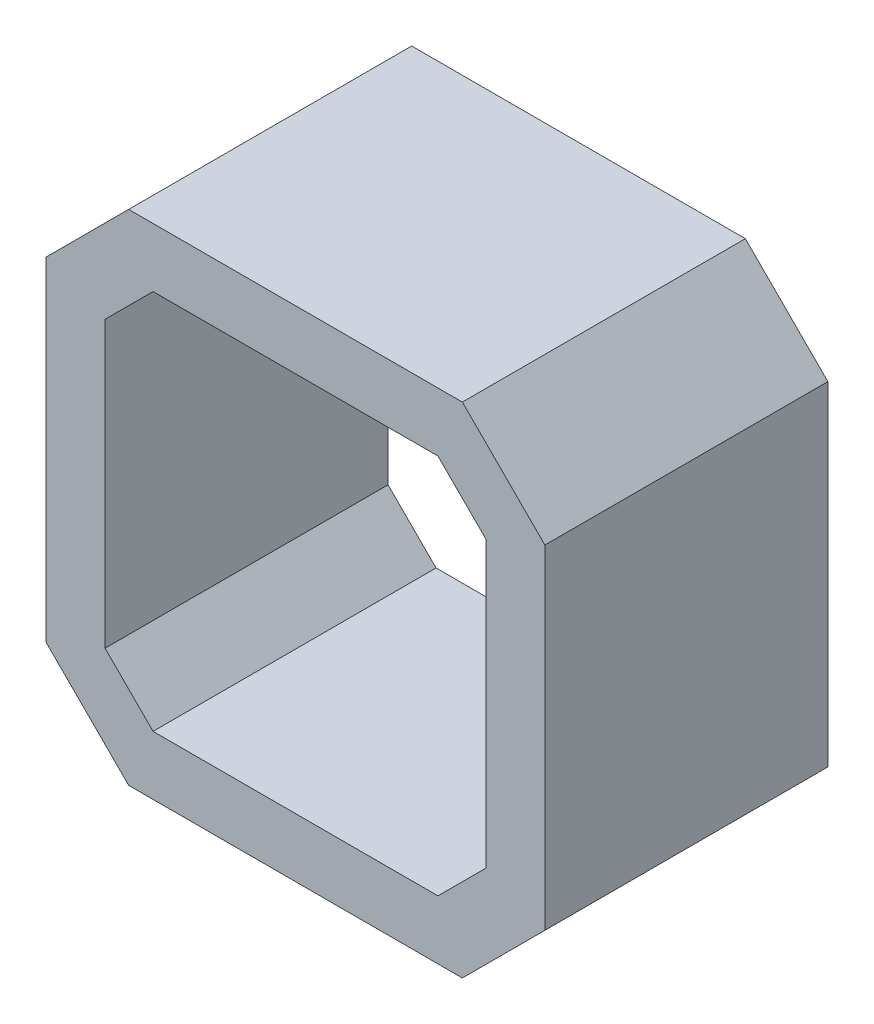
SolidWorks part; units mm, degrees
ref_plane "Front Plane" through (0, 0, 0) normal (0, 0, 1) x (1, 0, 0)
ref_plane "Top Plane" through (0, 0, 0) normal (0, 1, 0) x (1, 0, 0)
ref_plane "Right Plane" through (0, 0, 0) normal (1, 0, 0) x (0, 0, -1)
sketch "Sketch1" plane through (0, 0, 0) normal (0, 0, 1) x (1, 0, 0)
  line L0 (-21.15, 14.15) -> (-14.15, 21.15)
  line L1 (-14.15, -21.15) -> (14.15, -21.15)
  line L2 (-21.15, -14.15) -> (-21.15, 14.15)
  line L3 (-14.15, 21.15) -> (14.15, 21.15)
  line L4 (21.15, -14.15) -> (21.15, 14.15)
  line L5 (-21.15, -21.15) -> (21.15, 21.15) construction
  line L6 (-21.15, 21.15) -> (21.15, -21.15) construction
  line L7 (14.15, 21.15) -> (21.15, 14.15)
  line L8 (14.15, -21.15) -> (21.15, -14.15)
  line L9 (-21.15, -14.15) -> (-14.15, -21.15)
  line L10 (-12.0789, 16.15) -> (12.0789, 16.15)
  line L11 (12.0789, 16.15) -> (16.15, 12.0789)
  line L12 (16.15, -12.0789) -> (16.15, 12.0789)
  line L13 (12.0789, -16.15) -> (16.15, -12.0789)
  line L14 (-12.0789, -16.15) -> (12.0789, -16.15)
  line L15 (-16.15, -12.0789) -> (-12.0789, -16.15)
  line L16 (-16.15, -12.0789) -> (-16.15, 12.0789)
  line L17 (-16.15, 12.0789) -> (-12.0789, 16.15)
  point P0 (0, 0)
  dimension "D1" = 42.3
  dimension "D2" = 5
extrude "Boss-Extrude1" add sketch "Sketch1" along normal blind 24
